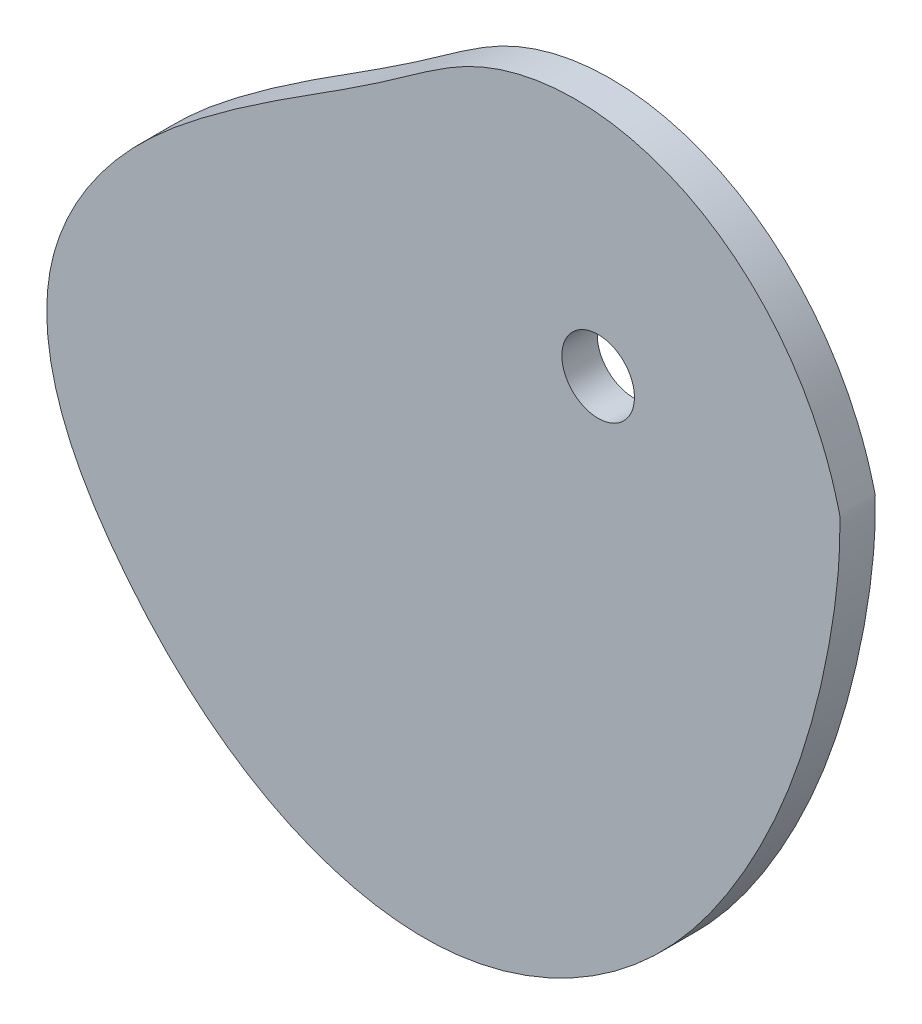
SolidWorks part; units mm, degrees
ref_plane "Front Plane" through (0, 0, 0) normal (0, 0, 1) x (1, 0, 0)
ref_plane "Top Plane" through (0, 0, 0) normal (0, 1, 0) x (1, 0, 0)
ref_plane "Right Plane" through (0, 0, 0) normal (1, 0, 0) x (0, 0, -1)
curve "Curve1"
sketch "Sketch1" plane through (0, 0, 0) normal (0, 0, 1) x (1, 0, 0)
  circle A0 centre (0, 0) radius 3.075
  spline S1 degree 3 number of poles 363 (20.4693, 0) -> (20.4693, 0)
  dimension "D1" = 6.15
extrude "Boss-Extrude1" add sketch "Sketch1" along normal mid plane 3
sketch "Sketch4" plane through (0, 0, 1.5) normal (0, 0, 1) x (1, 0, 0)
  line L0 (17.5773, -21.2942) -> (-0.4059, -51.7692) construction
  line L1 (-48.8051, -15.5697) -> (-20.0826, 24.9009) construction
  circle A0 centre (-13.2083, -15.9321) radius 29.2387 construction
  spline S0 degree 3 number of poles 363 (20.4693, 0) -> (20.4693, 0) construction
  point P5 (-13.488, -5.936)
  point P6 (-3.3675, -25.0764)
  point P11 (-25.0038, -24.2708)
  point P12 (-13.9531, -18.4277)
  dimension "D1" = 3
  dimension "D2" = 10
hole_wizard "M4 Clearance Hole1" [suppressed] positions "Sketch5" profile "Sketch7" hole size "M4" standard "ANSI Metric"
sketch "Sketch5" plane through (0, 0, 1.5) normal (0, 0, 1) x (1, 0, 0)
  point P0 (-13.488, -5.936)
  point P3 (-3.3675, -25.0764)
  point P6 (-25.0038, -24.2708)
sketch "Sketch7" plane through (-13.488, -5.936, 1.5) normal (1, 0, 0) x (0, -1, 0)
  line L0 (0, 0) -> (0, 3)
  line L1 (0, 3) -> (2.15, 3)
  line L2 (2.15, 3) -> (2.15, 0)
  line L5 (2.15, 0) -> (0, 0)
  line L11 (0, -6.35) -> (0, 107.95) construction
  dimension "Thru Hole Dia." = 4.3
  dimension "Thru Hole Depth" = 3
sketch "Sketch8" plane through (0, 0, 1.5) normal (0, 0, 1) x (1, 0, 0)
  line L5 (-11.09, -40.8947) -> (-20.9198, -47.7776) construction
  line L8 (-28.4462, -45.3019) -> (-27.0696, -47.2679)
  line L9 (-15.2394, -42.4024) -> (-16.8454, -40.1088)
  line L10 (-16.8454, -40.1088) -> (-27.0696, -47.2679)
  line L11 (-6.9178, -29.0068) -> (-3.3617, -34.0855) construction
  line L13 (-6.9178, -29.0068) -> (-18.7955, -37.3237)
  line L15 (-15.2394, -42.4024) -> (-3.3617, -34.0855)
  line L16 (-18.7955, -37.3237) -> (-18.222, -38.1428)
  line L17 (-18.222, -38.1428) -> (-28.4462, -45.3019)
  line L18 (-6.9178, -29.0068) -> (-6.5083, -28.72)
  line L19 (-6.5083, -28.72) -> (-2.9521, -33.7988)
  line L22 (-3.3617, -34.0855) -> (-2.9521, -33.7988)
  spline S1 degree 3 number of poles 363 (20.4693, 0) -> (20.4693, 0) construction
  dimension "D6" = 2.4
  dimension "D1" = 14.5
  dimension "D2" = 2.8
  dimension "D3" = 12
  dimension "D4" = 0.5
  dimension "D8" = 27
  dimension "D9" = 14.5
  dimension "D10" = 6.2
  dimension "D11" = 1
extrude "Cut-Extrude1" [suppressed] cut sketch "Sketch8" against normal through all both and the other way through all
fillet "Fillet1" [suppressed] radius 10
sketch "Sketch10" [suppressed] plane through (0, 0, 0) normal (0, 0, 1) x (1, 0, 0)
  line L1 (-8.5177, -31.4464) -> (-10.3214, -44.6038) construction
  line L2 (-22.8408, -43.8925) -> (-20.9018, -29.7487) construction
  line L3 (-8.5177, -31.4464) -> (-10.3214, -44.6038)
  line L4 (-22.8408, -43.8925) -> (-20.9018, -29.7487)
  circle A6 centre (-13.0442, -46.0588) radius 1.5
  arc A7 (-10.3214, -44.6038) -> (-7.077, -47.3226) centre (-7.8445, -44.9433) ccw construction
  arc A8 (-8.5177, -31.4464) -> (-20.9018, -29.7487) centre (-14.7098, -30.5976) ccw construction
  arc A9 (-26.388, -45.8122) -> (-22.8408, -43.8925) centre (-25.3176, -43.5529) ccw construction
  arc A10 (-10.3214, -44.6038) -> (-7.077, -47.3226) centre (-7.8445, -44.9433) ccw
  arc A11 (-8.5177, -31.4464) -> (-20.9018, -29.7487) centre (-14.7098, -30.5976) ccw
  arc A12 (-26.388, -45.8122) -> (-22.8408, -43.8925) centre (-25.3176, -43.5529) ccw
  spline S1 degree 3 number of poles 363 (-7.077, -47.3226) -> (-26.388, -45.8122) construction
  spline S2 degree 3 number of poles 213 (-7.077, -47.3226) -> (-26.388, -45.8122)
  spline S4 degree 3 number of poles 165 (-53.4212, -32.1303) -> (-53.4212, -32.1303)
  spline S5 degree 3 number of poles 165 (-53.4212, -32.1303) -> (-53.4212, -32.1303)
  dimension "D2" = 3
  dimension "D3" = 2.5
  dimension "D1" = 10
extrude "Boss-Extrude5" [suppressed] add sketch "Sketch10" along normal mid plane 1.5
sketch "Sketch11" [suppressed] plane through (0, 0, 0) normal (0, 0, 1) x (1, 0, 0)
  point P0 (-7.234, 7.8407)
  point P1 (10.4072, 2.3444)
  point P3 (-3.1732, -10.1851)
hole_wizard "M2x0.4 Tapped Hole1" [suppressed] positions "Sketch12" profile "Sketch13" tap size "M2x0.4" standard "ANSI Metric"
sketch "Sketch12" [suppressed] plane through (0, 0, -1.5) normal (0, 0, -1) x (-1, 0, 0)
  point P0 (7.234, 7.8407)
  point P3 (-10.4072, 2.3444)
  point P6 (3.1732, -10.1851)
sketch "Sketch13" plane through (-7.234, 7.8407, -1.5) normal (1, 0, 0) x (0, 1, 0)
  line L0 (0, 0) -> (0, 3)
  line L1 (0, 3) -> (0.7, 3)
  line L2 (0.7, 3) -> (0.7, 0)
  line L5 (0.7, 0) -> (0, 0)
  line L11 (0, -6.35) -> (0, 107.95) construction
  dimension "Thru Tap Drill Dia." = 1.4
  dimension "Thru Tap Drill Depth" = 3
cosmetic thread "Hole Thread1" [suppressed] parameters "D2"=2
cosmetic thread "Hole Thread2" [suppressed] parameters "D2"=2
cosmetic thread "Hole Thread3" [suppressed] parameters "D2"=2
fillet "Fillet2" [suppressed] radius 1.5
sketch "Sketch14" plane through (0, 0, 1.5) normal (0, 0, 1) x (1, 0, 0)
  circle A0 centre (-12.5246, -41.0492) radius 1.05 construction
  circle A1 centre (0, -39.819) radius 1.05
  dimension "D1" = 2.1
  dimension "D2" = 2.1
extrude "Cut-Extrude2" [suppressed] cut sketch "Sketch14" against normal through all
sketch "Sketch15" [suppressed] plane through (0, 0, 0.75) normal (0, 0, 1) x (1, 0, 0)
  circle A0 centre (-24.2994, -39.0947) radius 1.1
  circle A1 centre (-14.3282, -44.0575) radius 1.1
extrude "Cut-Extrude3" [suppressed] cut sketch "Sketch15" against normal blind 10
sketch "Sketch16" [suppressed] plane through (0, 0, 0.75) normal (0, 0, 1) x (1, 0, 0)
  circle A0 centre (-5.523, -52.2474) radius 1.15
  circle A1 centre (5.4449, -44.5935) radius 1.15
  dimension "D1" = 2.3
  dimension "D2" = 2.3
extrude "Cut-Extrude4" [suppressed] cut sketch "Sketch16" against normal blind 10
fillet "Fillet3" [suppressed] radius 0.4
fillet "Fillet4" [suppressed] radius 1.25
